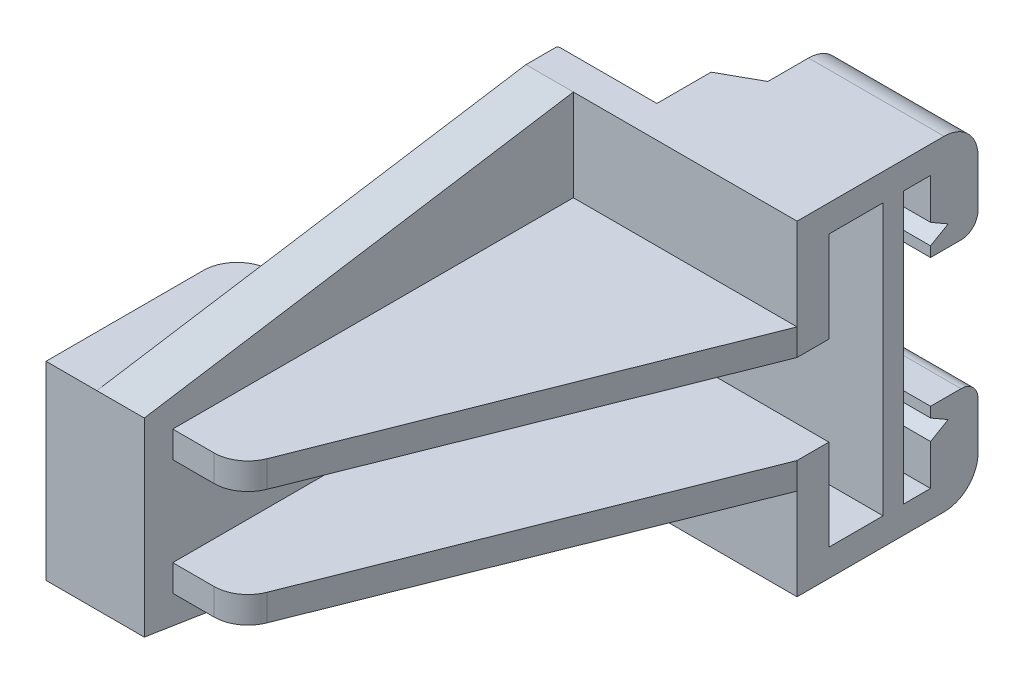
SolidWorks part; units mm, degrees
ref_plane "정면" through (0, 0, 0) normal (0, 0, 1) x (1, 0, 0)
ref_plane "윗면" through (0, 0, 0) normal (0, 1, 0) x (1, 0, 0)
ref_plane "우측면" through (0, 0, 0) normal (1, 0, 0) x (0, 0, -1)
sketch "스케치1" plane through (0, 0, 0) normal (1, 0, 0) x (0, 0, -1)
  line L1 (0, 0) -> (90, 0)
  line L2 (0, 0) -> (0, 48)
  line L3 (0, 48) -> (90, 48)
  line L4 (90, 0) -> (90, 48)
  dimension "D1" = 48
  dimension "D2" = 90
extrude "보스-돌출1" add sketch "스케치1" along normal blind 40
sketch "스케치2" plane through (40, 0, 0) normal (1, 0, 0) x (0, 0, -1)
  line L0 (90, 48) -> (0, 48) construction
  line L1 (79, 44) -> (83, 44)
  line L2 (79, 44) -> (79, 4)
  line L3 (79, 4) -> (83, 4)
  line L4 (83, 44) -> (83, 38)
  line L5 (0, 0) -> (90, 0) construction
  line L6 (90, 0) -> (90, 48) construction
  line L7 (83, 38) -> (85.5981, 36.5)
  line L8 (85.5981, 36.5) -> (83, 35)
  line L9 (-9.108, 24) -> (98.6493, 24) construction
  line L10 (85.5981, 11.5) -> (83, 13)
  line L11 (83, 10) -> (85.5981, 11.5)
  line L12 (83, 35) -> (83, 33.5)
  line L13 (83, 10) -> (83, 4)
  line L14 (83, 14.5) -> (83, 13)
  line L15 (83, 33.5) -> (90, 33.5)
  line L17 (83, 14.5) -> (90, 14.5)
  line L18 (90, 33.5) -> (90, 14.5)
  line L19 (0, 38) -> (63.304, 48)
  line L20 (0, 48) -> (0, 0) construction
  line L21 (63.304, 48) -> (0, 48)
  line L22 (0, 48) -> (0, 38)
  line L23 (0, 10) -> (63.304, 0)
  line L24 (63.304, 0) -> (0, 0)
  line L25 (0, 0) -> (0, 10)
  dimension "D1" = 4
  dimension "D2" = 4
  dimension "D3" = 4
  dimension "D4" = 7
  dimension "D5" = 60
  dimension "D6" = 3
  dimension "D7" = 60
  dimension "D8" = 14.5
  dimension "D9" = 6
  dimension "D10" = 14.5
extrude "컷-돌출1" cut sketch "스케치2" against normal blind 40
sketch "스케치3" plane through (0, 48, 0) normal (0, 1, 0) x (1, 0, 0)
  line L0 (0, 67.8468) -> (20, 79)
  line L1 (0, 90) -> (0, 63.304) construction
  line L2 (20, 79) -> (20, 90)
  line L4 (20, 90) -> (0, 90)
  line L5 (0, 90) -> (0, 67.8468)
extrude "컷-돌출2" cut sketch "스케치3" against normal through all
sketch "스케치4" plane through (0, 48, 0) normal (0, 1, 0) x (1, 0, 0)
  line L0 (40, 63.304) -> (14.8076, 0)
  line L1 (0, 0) -> (40, 0) construction
  line L2 (14.8076, 0) -> (40, 0)
  line L3 (40, 0) -> (40, 63.304)
extrude "컷-돌출3" cut sketch "스케치4" against normal through all
sketch "스케치5" plane through (40, 0, 0) normal (1, 0, 0) x (0, 0, -1)
  line L0 (-7.1778, 24) -> (95.0444, 24) construction
  line L1 (63.304, 0) -> (63.304, 48) construction
  line L2 (4.2, 34.4889) -> (63.304, 34.4889)
  line L3 (4.2, 34.4889) -> (4.2, 30.5778)
  line L4 (4.2, 30.5778) -> (63.304, 30.5778)
  line L6 (4.2, 17.4222) -> (63.304, 17.4222)
  line L8 (4.2, 13.5111) -> (63.304, 13.5111)
  line L9 (4.2, 13.5111) -> (4.2, 17.4222)
  line L10 (63.304, 34.4889) -> (63.304, 48)
  line L11 (63.304, 48) -> (0, 38)
  line L12 (0, 38) -> (0, 10)
  line L13 (0, 10) -> (63.304, 0)
  line L14 (63.304, 0) -> (63.304, 13.5111)
  line L15 (63.304, 30.5778) -> (63.304, 17.4222)
extrude "컷-돌출4" cut sketch "스케치5" against normal blind 33
sketch "스케치6" plane through (40, 0, 0) normal (1, 0, 0) x (0, 0, -1)
  line L0 (79, 44) -> (79, 4) construction
  line L1 (76, 44) -> (68, 44)
  line L2 (76, 44) -> (76, 4)
  line L3 (76, 4) -> (68, 4)
  line L4 (68, 44) -> (68, 4)
  dimension "D1" = 3
  dimension "D2" = 8
extrude "컷-돌출5" cut sketch "스케치6" against normal through all
sketch "스케치7" plane through (0, 0, -63.304) normal (0, 0, 1) x (1, 0, 0)
  line L0 (7, 30.5778) -> (40, 30.5778) construction
  line L1 (20, 30.5778) -> (40, 30.5778)
  line L2 (20, 30.5778) -> (20, 17.4222)
  line L3 (20, 17.4222) -> (40, 17.4222)
  line L4 (40, 30.5778) -> (40, 17.4222)
extrude "컷-돌출6" cut sketch "스케치7" against normal blind 5
sketch "스케치8" plane through (0, 0, 0) normal (-1, 0, 0) x (0, 0, 1)
  line L1 (0, 38) -> (-28.2, 38)
  line L2 (0, 38) -> (0, 10)
  line L3 (0, 10) -> (-28.2, 10)
  line L4 (-28.2, 38) -> (-28.2, 10)
extrude "보스-돌출2" add sketch "스케치8" along normal blind 7.5
sketch "스케치9" plane through (0, 0, -79) normal (0, 0, -1) x (-1, 0, 0)
  circle A0 centre (-30, 24) radius 2.25
  dimension "D1" = 4.5
extrude "보스-돌출3" add sketch "스케치9" along normal blind 4
sketch "스케치10" plane through (0, 0, -83) normal (0, 0, -1) x (-1, 0, 0)
  circle A0 centre (-30, 24) radius 1.2
  dimension "D1" = 2.4
extrude "컷-돌출7" cut sketch "스케치10" against normal through all
fillet "필렛1" radius 5 5 edges at (-7.5, 24, -28.2) (16.479, 15.4667, -4.2) (16.479, 32.5333, -4.2) (30, 0, -90) (30, 48, -90)
fillet "필렛2" radius 2.5 2 edges at (30, 14.5, -90) (30, 33.5, -90)
sketch "스케치11" plane through (0, 0, -68) normal (0, 0, -1) x (-1, 0, 0)
  line L0 (0, 0) -> (-20, 0) construction
  line L1 (0, 48) -> (-14.6204, 48)
  line L2 (0, 48) -> (0, 0)
  line L3 (0, 0) -> (-14.6204, 0)
  line L4 (-14.6204, 48) -> (-14.6204, 0)
extrude "컷-돌출8" cut sketch "스케치11" along normal blind 10
